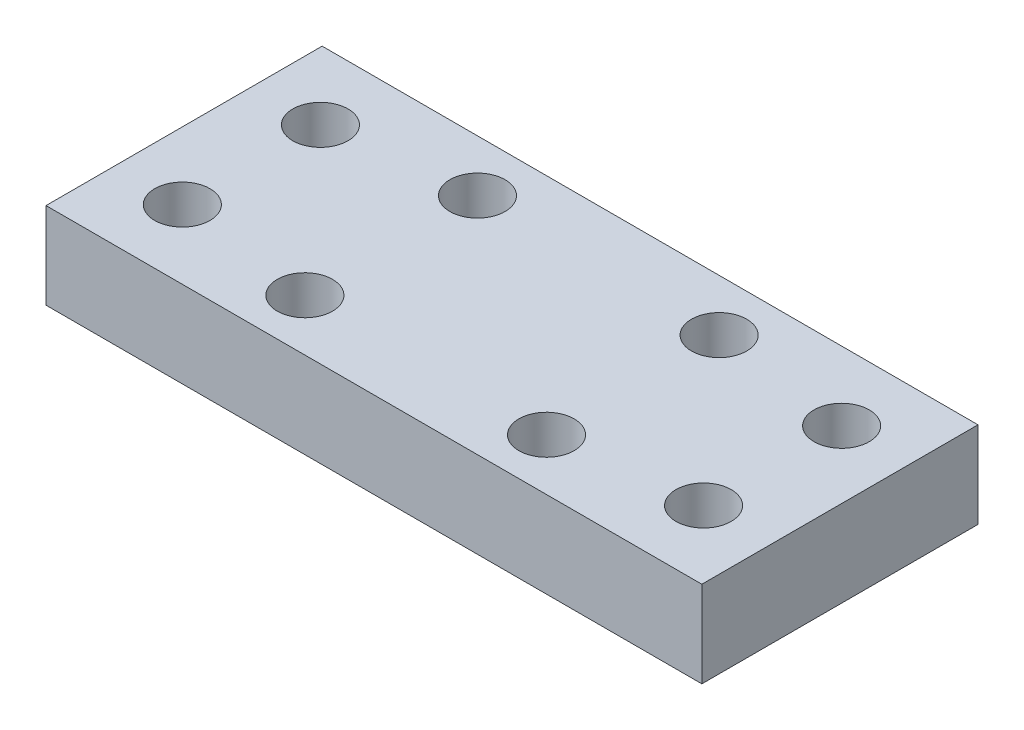
SolidWorks part; units mm, degrees
ref_plane "Front Plane" through (0, 0, 0) normal (0, 0, 1) x (1, 0, 0)
ref_plane "Top Plane" through (0, 0, 0) normal (0, 1, 0) x (1, 0, 0)
ref_plane "Right Plane" through (0, 0, 0) normal (1, 0, 0) x (0, 0, -1)
sketch "Sketch1" plane through (0, 0, 0) normal (0, 1, 0) x (1, 0, 0)
  line L0 (-24.3855, -4) -> (28.0345, -4) construction
  line L1 (-19, 4) -> (19, 4)
  line L2 (-19, 4) -> (-19, -4)
  line L4 (19, 4) -> (19, -12)
  line L5 (-19, -12) -> (-19, -4)
  line L6 (-19, -12) -> (19, -12)
  circle A0 centre (-7, 1) radius 1.6
  circle A1 centre (7, 1) radius 1.6
  circle A2 centre (15.1, 0) radius 1.6
  circle A3 centre (-15.1, 0) radius 1.6
  circle A4 centre (-15.1, -8) radius 1.6
  circle A5 centre (15.1, -8) radius 1.6
  circle A6 centre (7, -9) radius 1.6
  circle A7 centre (-7, -9) radius 1.6
  point P4 (0, 4)
  point P6 (-19, 0)
  dimension "D3" = 3.2
  dimension "D4" = 7
  dimension "D5" = 7
  dimension "D6" = 15.1
  dimension "D8" = 1
  dimension "D1" = 38
  dimension "D2" = 8
  dimension "D7" = 15.1
extrude "Boss-Extrude1" add sketch "Sketch1" along normal blind 5
